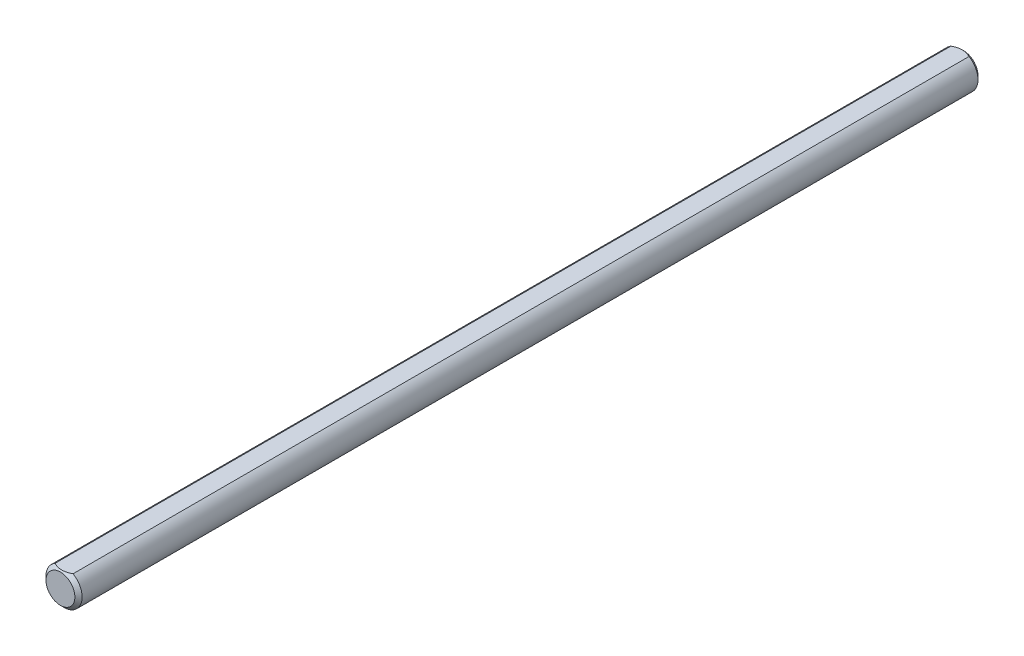
SolidWorks part; units mm, degrees
ref_plane "Front" through (0, 0, 0) normal (0, 0, 1) x (1, 0, 0)
ref_plane "Top" through (0, 0, 0) normal (0, 1, 0) x (1, 0, 0)
ref_plane "Right" through (0, 0, 0) normal (1, 0, 0) x (0, 0, -1)
sketch "Sketch1" plane through (0, 0, 0) normal (0, 0, 1) x (1, 0, 0)
  circle A0 centre (0, 0) radius 3.175
  dimension "D1" = 6.35
extrude "Extrude1" add sketch "Sketch1" along normal mid plane 158.75
chamfer "Chamfer1" distance 0.635 angle 45 2 edges at (3.175, 0, -79.375) (3.175, 0, 79.375)
sketch "Sketch13" plane through (0, 0, 0) normal (0, 0, 1) x (1, 0, 0)
  line L3 (-1.5875, 2.7496) -> (1.5875, 2.7496)
  circle A0 centre (0, 0) radius 3.175 construction
  arc A1 (1.5875, 2.7496) -> (-1.5875, 2.7496) centre (0, 0) ccw
  dimension "D1" = 3.175
extrude "Extrude7" cut sketch "Sketch13" against normal through all and the other way through all
equation "\"D1@Chamfer1\" = \"D1@Sketch1\" * .1"
equation "\"D1@Sketch13\" = \"D1@Sketch1\" * .5"
